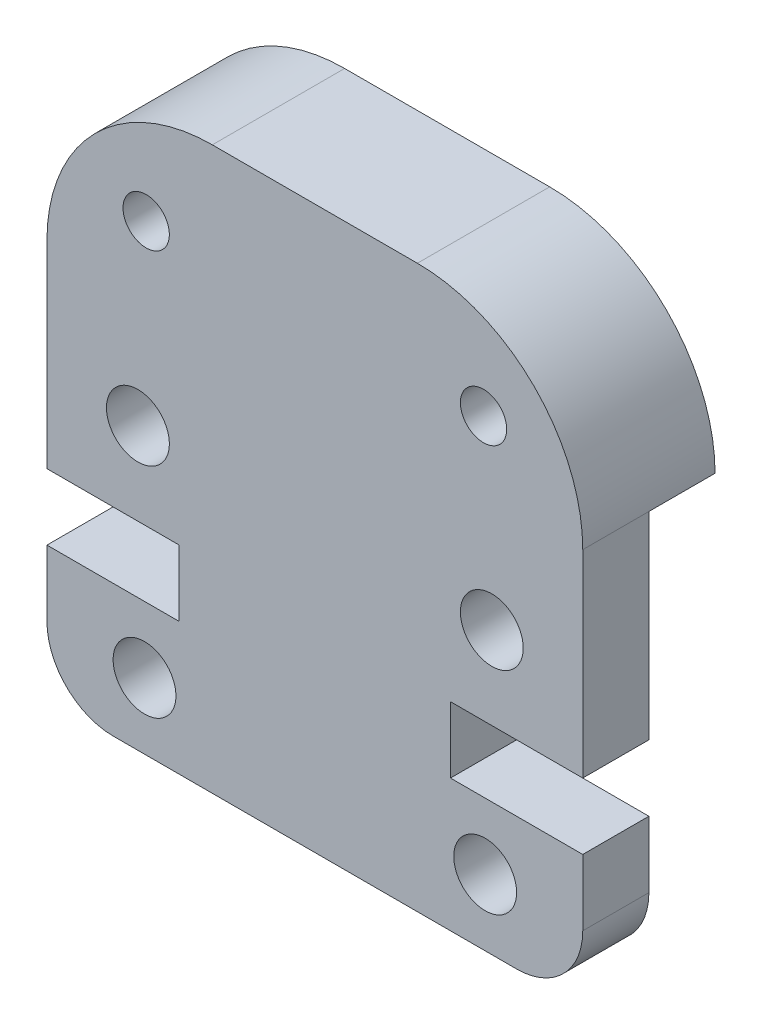
SolidWorks part; units mm, degrees
ref_plane "Front Plane" through (0, 0, 0) normal (0, 0, 1) x (1, 0, 0)
ref_plane "Top Plane" through (0, 0, 0) normal (0, 1, 0) x (1, 0, 0)
ref_plane "Right Plane" through (0, 0, 0) normal (1, 0, 0) x (0, 0, -1)
sketch "Sketch1" plane through (0, 0, 0) normal (0, 0, 1) x (1, 0, 0)
  line L0 (0, 16.98) -> (0, 0) construction
  line L1 (3.1, 16.98) -> (-3.1, 16.98)
  line L2 (6.1, 0) -> (-6.1, 0)
  line L3 (-8.1, 6) -> (-4.1, 6)
  line L4 (-4.1, 6) -> (-4.1, 4)
  line L5 (-4.1, 4) -> (-8.1, 4)
  line L6 (-8.1, 2) -> (-8.1, 4)
  line L7 (8.1, 11.98) -> (8.1, 6)
  line L8 (-8.1, 11.98) -> (-8.1, 6)
  line L24 (8.1, 2) -> (8.1, 4)
  line L27 (4.1, 4) -> (8.1, 4)
  line L30 (4.1, 6) -> (4.1, 4)
  line L31 (8.1, 6) -> (4.1, 6)
  circle A0 centre (-5.15, 2) radius 0.95
  circle A1 centre (-5.1, 13.98) radius 0.7
  arc A2 (-8.1, 11.98) -> (-3.1, 16.98) centre (-3.1, 11.98) cw
  arc A3 (-6.1, 0) -> (-8.1, 2) centre (-6.1, 2) cw
  circle A4 centre (-5.35, 8.5) radius 0.95
  circle A10 centre (5.35, 8.5) radius 0.95
  arc A12 (6.1, 0) -> (8.1, 2) centre (6.1, 2) ccw
  arc A14 (8.1, 11.98) -> (3.1, 16.98) centre (3.1, 11.98) ccw
  circle A16 centre (5.1, 13.98) radius 0.7
  circle A18 centre (5.15, 2) radius 0.95
  dimension "D1" = 1.9
  dimension "D2" = 1.4
  dimension "D3" = 16.98
  dimension "D4" = 2
  dimension "D5" = 5
  dimension "D6" = 6.1
  dimension "D7" = 3
  dimension "D8" = 3
  dimension "D9" = 2.75
  dimension "D10" = 8.5
extrude "Boss-Extrude1" add sketch "Sketch1" along normal blind 4
sketch "Sketch2" plane through (0, 0, 0) normal (0, 0, 1) x (1, 0, 0)
  line L0 (-8.1, 0) -> (8.1, 0)
  line L1 (8.1, 0) -> (8.1, 11.98)
  line L2 (8.1, 11.98) -> (-8.1, 11.98)
  line L3 (-8.1, 11.98) -> (-8.1, 0)
extrude "Cut-Extrude1" cut sketch "Sketch2" along normal blind 2
equation "\"D6@Sketch1\"= ( \"fingerWidth@parametersSketch@prostheticParameters.SLDPRT\" - 4 ) / 2'Finger Width - Radius"
equation "\"D3@Sketch1\"= ( \"HL@parametersSketch@prostheticParameters.SLDPRT\" * 0.108 ) - 3 'DIP Legth-Sil. Sh. DIP"
equation "\"D1@Sketch1\"= 1.5 + \"tol1@parametersSketch@prostheticParameters.SLDPRT\""
equation "\"D2@Sketch1\"= 1 + \"tol1@parametersSketch@prostheticParameters.SLDPRT\""
